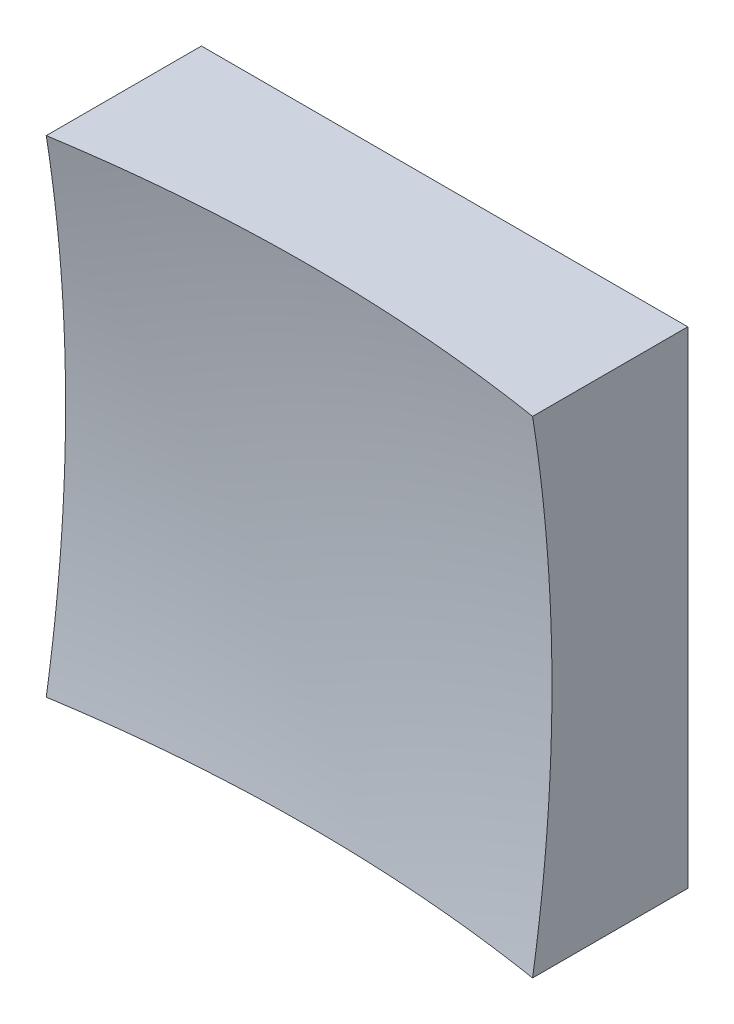
SolidWorks part; units mm, degrees
ref_plane "前视基准面" through (0, 0, 0) normal (0, 0, 1) x (1, 0, 0)
ref_plane "上视基准面" through (0, 0, 0) normal (0, 1, 0) x (1, 0, 0)
ref_plane "右视基准面" through (0, 0, 0) normal (1, 0, 0) x (0, 0, -1)
sketch "草图1" plane through (0, 0, 0) normal (0, 0, 1) x (1, 0, 0)
  line L1 (-6.25, 6.25) -> (6.25, 6.25)
  line L2 (-6.25, 6.25) -> (-6.25, -6.25)
  line L3 (-6.25, -6.25) -> (6.25, -6.25)
  line L4 (6.25, 6.25) -> (6.25, -6.25)
  line L5 (-6.25, 6.25) -> (6.25, -6.25) construction
  line L6 (-6.25, -6.25) -> (6.25, 6.25) construction
  point P0 (0, 0)
  dimension "D1" = 12.5
  dimension "D2" = 12.5
extrude "凸台-拉伸1" add sketch "草图1" along normal blind 10 contours L2 L3 L4 L1
sketch "草图2" plane through (0, 0, 0) normal (0, 1, 0) x (1, 0, 0)
  line L0 (-7.4603, -3) -> (7.3192, -3) construction
  line L1 (0, 0) -> (0, -12.1749) construction
  line L2 (38.9938, -34.0847) -> (0, -34.0847)
  line L3 (0, -34.0847) -> (0, -3)
  arc A1 (38.9938, -34.0847) -> (0, -3) centre (0, -43) ccw
  dimension "D2" = 80
  dimension "D1" = 3
revolve "切除-旋转2" cut sketch "草图2" angle 360 about L3
